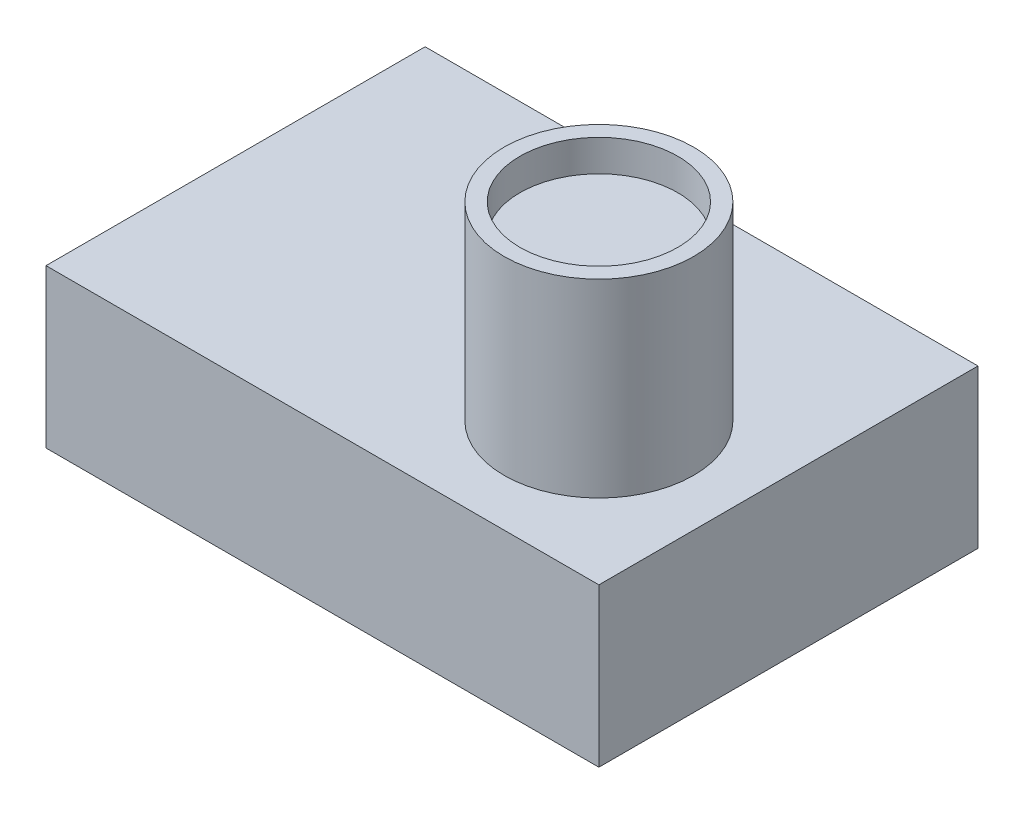
SolidWorks part; units mm, degrees
material "1060 Alloy"
ref_plane "Front Plane" through (0, 0, 0) normal (0, 0, 1) x (1, 0, 0)
ref_plane "Top Plane" through (0, 0, 0) normal (0, 1, 0) x (1, 0, 0)
ref_plane "Right Plane" through (0, 0, 0) normal (1, 0, 0) x (0, 0, -1)
sketch "Sketch2" plane through (0, 0, 0) normal (0, 1, 0) x (1, 0, 0)
  line L1 (-17.5, 12) -> (17.5, 12)
  line L2 (-17.5, 12) -> (-17.5, -12)
  line L3 (-17.5, -12) -> (17.5, -12)
  line L4 (17.5, 12) -> (17.5, -12)
  line L5 (-17.5, 12) -> (17.5, -12) construction
  line L6 (-17.5, -12) -> (17.5, 12) construction
  point P0 (0, 0)
  dimension "D1" = 35
  dimension "D2" = 24
extrude "Boss-Extrude1" add sketch "Sketch2" along normal blind 10
sketch "Sketch3" plane through (0, 10, 0) normal (0, 1, 0) x (1, 0, 0)
  line L0 (17.5, -12) -> (17.5, 12) construction
  line L1 (-17.5, -12) -> (17.5, -12) construction
  circle A0 centre (8.5, -3) radius 6
  dimension "D1" = 12
  dimension "D2" = 9
  dimension "D3" = 9
extrude "Boss-Extrude2" add sketch "Sketch3" along normal blind 12
sketch "Sketch4" plane through (0, 22, 0) normal (0, 1, 0) x (1, 0, 0)
  circle A0 centre (8.5, -3) radius 5
  circle A1 centre (8.5, -3) radius 6 construction
  dimension "D1" = 10
extrude "Cut-Extrude2" cut sketch "Sketch4" against normal blind 2
